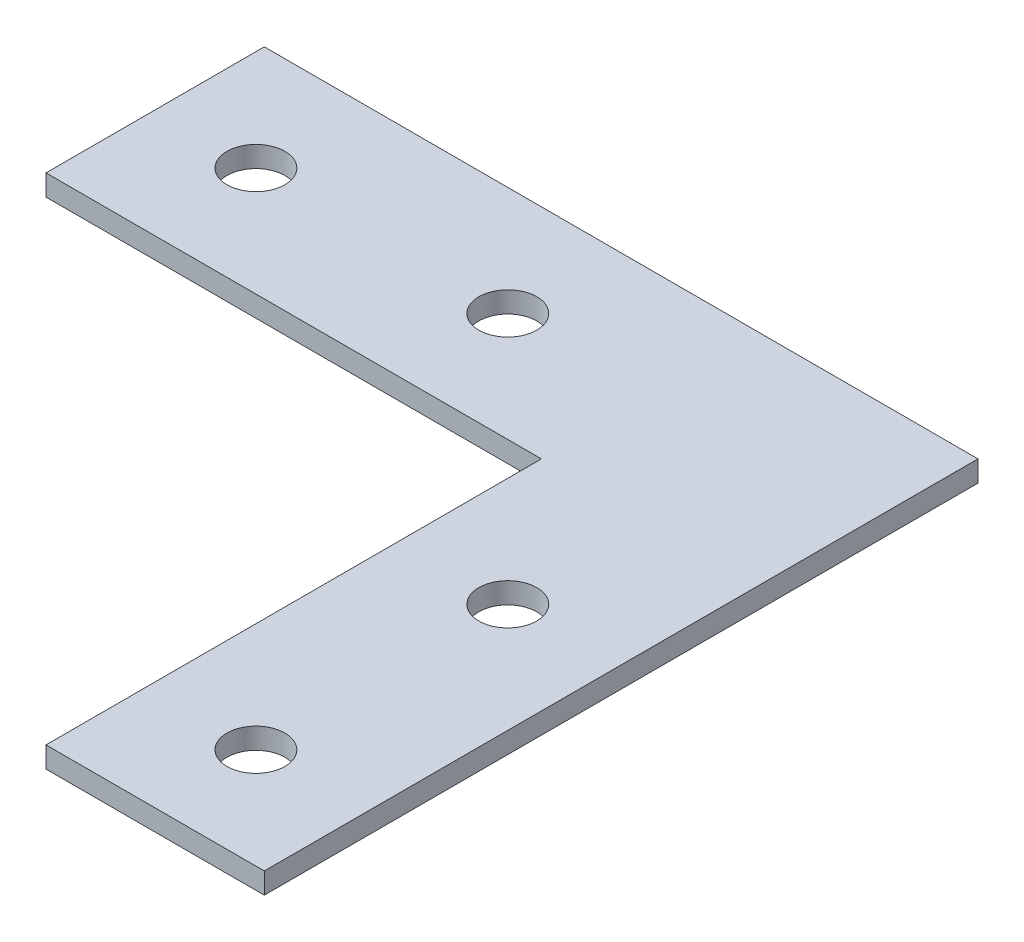
SolidWorks part; units mm, degrees
material "201 退火不锈钢 (SS)"
ref_plane "前视基准面" through (0, 0, 0) normal (0, 0, 1) x (1, 0, 0)
ref_plane "上视基准面" through (0, 0, 0) normal (0, 1, 0) x (1, 0, 0)
ref_plane "右视基准面" through (0, 0, 0) normal (1, 0, 0) x (0, 0, -1)
sketch "草图1" plane through (0, 0, 0) normal (0, 1, 0) x (1, 0, 0)
  line L0 (0, 0) -> (0, -59)
  line L1 (0, -59) -> (26, -59)
  line L2 (26, -59) -> (26, 26)
  line L3 (26, 26) -> (-59, 26)
  line L4 (-59, 26) -> (-59, 0)
  line L5 (-59, 0) -> (0, 0)
  line L6 (-59, 13) -> (26, 13) construction
  line L7 (13, -59) -> (13, 26) construction
  circle A0 centre (-47, 13) radius 3.45
  circle A1 centre (-17, 13) radius 3.45
  circle A2 centre (13, -47) radius 3.45
  circle A3 centre (13, -17) radius 3.45
  dimension "D5" = 6.9
  dimension "D6" = 6.9
  dimension "D7" = 12
  dimension "D8" = 30
  dimension "D9" = 6.9
  dimension "D10" = 6.9
  dimension "D11" = 12
  dimension "D12" = 30
  dimension "D1" = 85
  dimension "D2" = 85
  dimension "D3" = 26
  dimension "D4" = 26
extrude "凸台-拉伸1" add sketch "草图1" along normal blind 2.5
